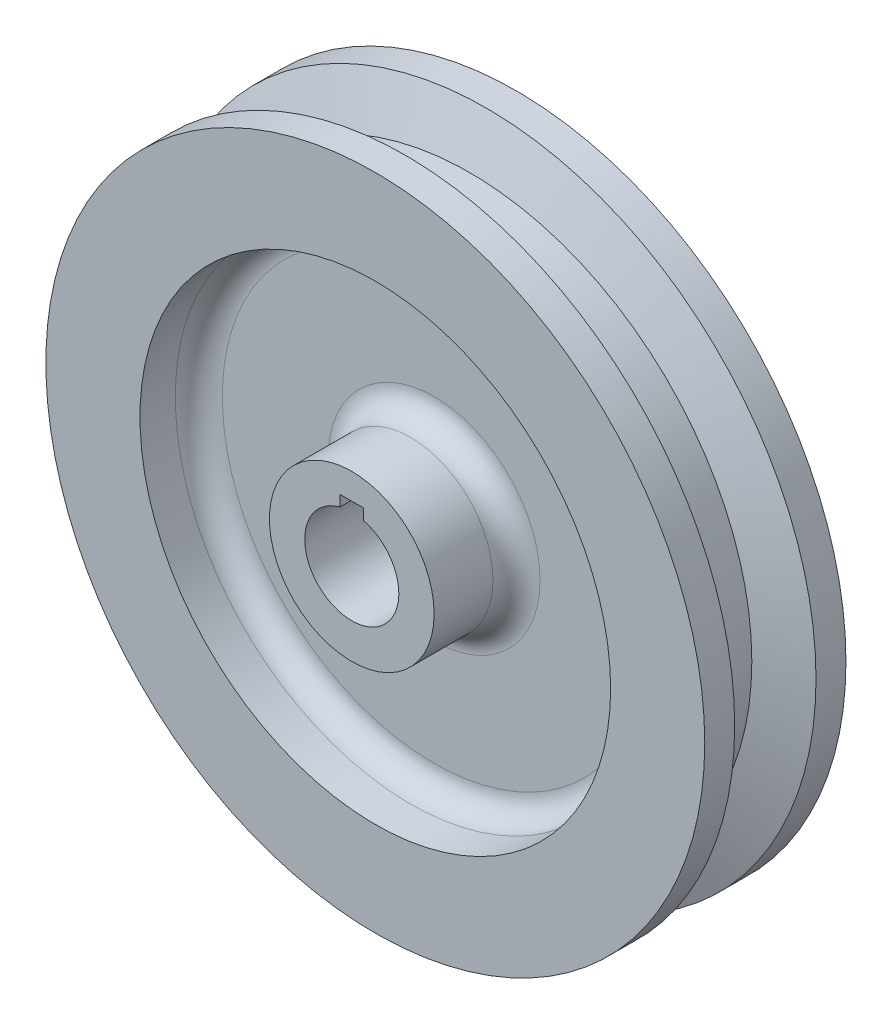
SolidWorks part; units mm, degrees
material "Cast Carbon Steel"
ref_plane "Front Plane" through (0, 0, 0) normal (0, 0, 1) x (1, 0, 0)
ref_plane "Top Plane" through (0, 0, 0) normal (0, 1, 0) x (1, 0, 0)
ref_plane "Right Plane" through (0, 0, 0) normal (1, 0, 0) x (0, 0, -1)
sketch "Sketch1" plane through (0, 0, 0) normal (1, 0, 0) x (0, 0, -1)
  line L0 (0, 0) -> (0, 41.4379) construction
  line L1 (0, 0) -> (42.7808, 0) construction
  line L2 (25.4, 22.225) -> (-25.4, 22.225)
  line L3 (25.4, 22.225) -> (25.4, 12.7)
  line L4 (25.4, 12.7) -> (-25.4, 12.7)
  line L5 (-25.4, 22.225) -> (-25.4, 12.7)
  line L6 (25.4, 22.225) -> (-25.4, 12.7) construction
  line L7 (25.4, 12.7) -> (-25.4, 22.225) construction
  line L8 (19.05, 88.9) -> (-19.05, 88.9)
  line L9 (19.05, 88.9) -> (19.05, 63.5)
  line L10 (19.05, 63.5) -> (-19.05, 63.5)
  line L11 (-19.05, 88.9) -> (-19.05, 63.5)
  line L12 (19.05, 88.9) -> (-19.05, 63.5) construction
  line L13 (19.05, 63.5) -> (-19.05, 88.9) construction
  line L14 (-3.175, 22.225) -> (3.175, 22.225)
  line L15 (-3.175, 22.225) -> (-3.175, 63.5)
  line L16 (-3.175, 63.5) -> (3.175, 63.5)
  line L17 (3.175, 22.225) -> (3.175, 63.5)
  point P3 (0, 17.4625)
  point P8 (0, 76.2)
  dimension "D1" = 38.1
  dimension "D2" = 50.8
  dimension "D3" = 6.35
  dimension "D4" = 177.8
  dimension "D5" = 127
  dimension "D6" = 44.45
  dimension "D7" = 25.4
revolve "Revolve1" add sketch "Sketch1" angle 360 about L1
sketch "Sketch3" plane through (0, 0, 0) normal (1, 0, 0) x (0, 0, -1)
  line L0 (0, 0) -> (100.7407, 0) construction
  line L1 (0, 0) -> (0, 98.7832) construction
  line L2 (19.05, 88.9) -> (-19.05, 88.9) construction
  line L3 (-10.9724, 88.9) -> (10.9724, 88.9)
  line L4 (10.9724, 88.9) -> (6.35, 76.2)
  line L5 (6.35, 76.2) -> (-6.35, 76.2)
  line L6 (-6.35, 76.2) -> (-10.9724, 88.9)
  dimension "D1" = 40
  dimension "D2" = 12.7
  dimension "D3" = 12.7
revolve "Cut-Revolve1" cut sketch "Sketch3" angle 360 about L0
fillet "Fillet1" radius 6.35 4 edges at (63.5, 0, -3.175) (22.225, 0, -3.175) (63.5, 0, 3.175) (22.225, 0, 3.175)
sketch "Sketch4" plane through (0, 0, 25.4) normal (0, 0, 1) x (1, 0, 0)
  line L1 (3.175, 0) -> (-3.175, 0)
  line L2 (3.175, 0) -> (3.175, 15.24)
  line L3 (3.175, 15.24) -> (-3.175, 15.24)
  line L4 (-3.175, 0) -> (-3.175, 15.24)
  dimension "D1" = 15.24
  dimension "D2" = 6.35
extrude "Cut-Extrude1" cut sketch "Sketch4" against normal through all
